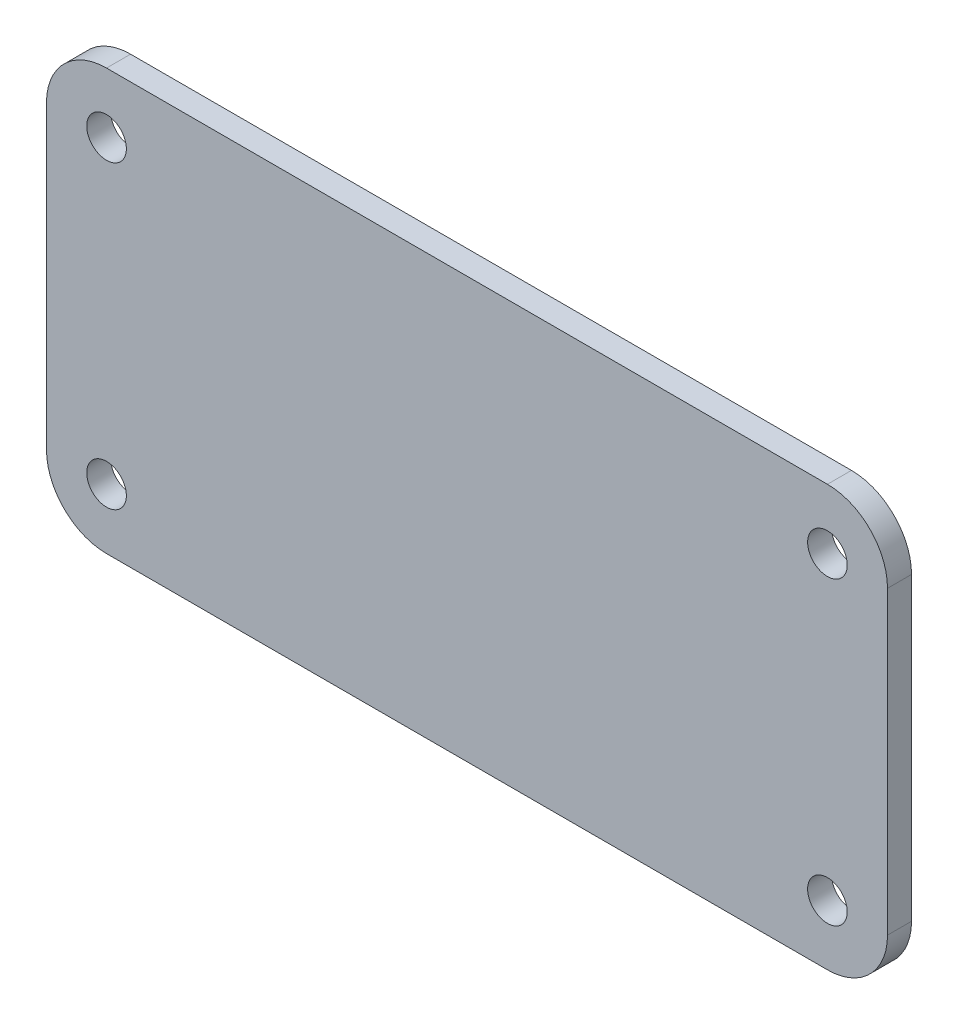
SolidWorks part; units mm, degrees
ref_plane "前视基准面" through (0, 0, 0) normal (0, 0, 1) x (1, 0, 0)
ref_plane "上视基准面" through (0, 0, 0) normal (0, 1, 0) x (1, 0, 0)
ref_plane "右视基准面" through (0, 0, 0) normal (1, 0, 0) x (0, 0, -1)
sketch "草图1" plane through (0, 0, 0) normal (0, 0, 1) x (1, 0, 0)
  line L1 (0, 0) -> (70, 0)
  line L2 (0, 0) -> (0, 35)
  line L3 (0, 35) -> (70, 35)
  line L4 (70, 0) -> (70, 35)
  dimension "D1" = 70
  dimension "D2" = 35
extrude "凸台-拉伸1" add sketch "草图1" along normal blind 2
fillet "圆角1" radius 5 4 edges at (0, 0, 1) (70, 0, 1) (70, 35, 1) (0, 35, 1)
sketch "草图2" plane through (0, 0, 2) normal (0, 0, 1) x (1, 0, 0)
  line L4 (0, 30) -> (0, 5)
  line L5 (5, 0) -> (65, 0)
  line L6 (70, 5) -> (70, 30)
  line L7 (65, 35) -> (5, 35)
  line L8 (0, 30) -> (0, 5)
  line L9 (5, 0) -> (65, 0)
  line L10 (70, 5) -> (70, 30)
  line L11 (65, 35) -> (5, 35)
  circle A0 centre (5, 30) radius 1.65
  circle A1 centre (5, 5) radius 1.65
  circle A2 centre (65, 5) radius 1.65
  circle A3 centre (65, 30) radius 1.65
  arc A4 (0, 5) -> (5, 0) centre (5, 5) ccw
  arc A5 (65, 0) -> (70, 5) centre (65, 5) ccw
  arc A6 (70, 30) -> (65, 35) centre (65, 30) ccw
  arc A7 (5, 35) -> (0, 30) centre (5, 30) ccw
  arc A8 (0, 5) -> (5, 0) centre (5, 5) ccw
  arc A9 (65, 0) -> (70, 5) centre (65, 5) ccw
  arc A10 (70, 30) -> (65, 35) centre (65, 30) ccw
  arc A11 (5, 35) -> (0, 30) centre (5, 30) ccw
  dimension "D2" = 3.3
  dimension "D3" = 3.3
  dimension "D4" = 3.3
  dimension "D5" = 3.3
  dimension "D1" = 0
extrude "切除-拉伸1" cut sketch "草图2" against normal blind 2 contours A0 | A1 | A3 | A2
